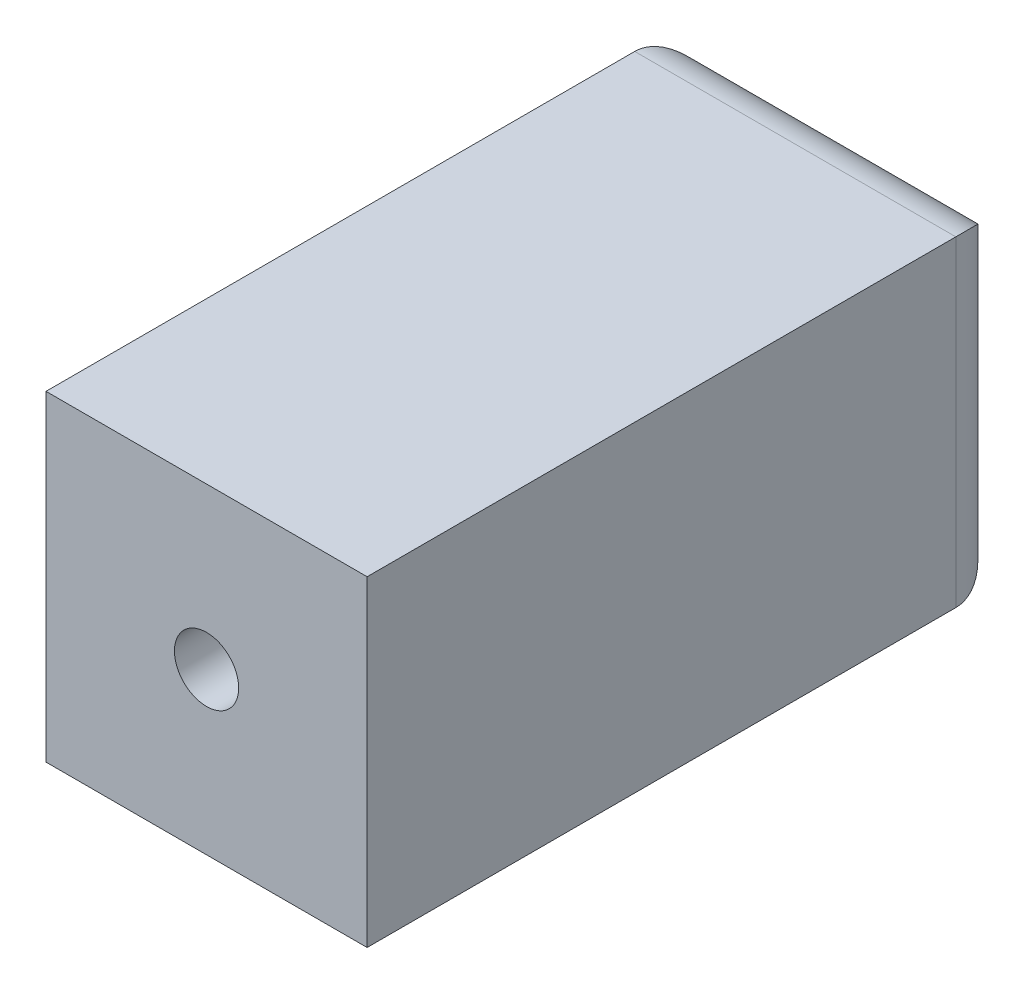
SolidWorks part; units mm, degrees
ref_plane "Front Plane" through (0, 0, 0) normal (0, 0, 1) x (1, 0, 0)
ref_plane "Top Plane" through (0, 0, 0) normal (0, 1, 0) x (1, 0, 0)
ref_plane "Right Plane" through (0, 0, 0) normal (1, 0, 0) x (0, 0, -1)
sketch "Sketch1" plane through (0, 0, 0) normal (0, 0, 1) x (1, 0, 0)
  line L1 (0, 0) -> (15, 0)
  line L2 (0, 0) -> (0, 15)
  line L3 (0, 15) -> (15, 15)
  line L4 (15, 0) -> (15, 15)
  dimension "D1" = 15
  dimension "D2" = 15
extrude "Boss-Extrude1" add sketch "Sketch1" along normal blind 30
fillet "Fillet2" radius 2.5 4 edges at (7.5, 0, 0) (15, 7.5, 0) (7.5, 15, 0) (0, 7.5, 0)
hole_wizard "M3x0.5 Tapped Hole1" positions "Sketch3" profile "Sketch4" tap size "M3x0.5" standard "ANSI Metric" end condition through all
sketch "Sketch3" plane through (0, 0, 0) normal (0, 0, -1) x (-1, 0, 0)
  line L0 (-7.5, 2.5) -> (-7.5, 12.5) construction
  line L1 (-12.5, 2.5) -> (-2.5, 2.5) construction
  line L2 (-2.5, 12.5) -> (-12.5, 12.5) construction
  line L5 (-12.5, 7.5) -> (-2.5, 7.5) construction
  line L6 (-12.5, 12.5) -> (-12.5, 2.5) construction
  line L7 (-2.5, 2.5) -> (-2.5, 12.5) construction
  point P20 (-7.5, 7.5)
sketch "Sketch4" plane through (7.5, 7.5, 0) normal (1, 0, 0) x (0, 1, 0)
  line L0 (0, 0) -> (0, 30)
  line L1 (0, 30) -> (1.5, 30)
  line L2 (1.5, 30) -> (1.5, 0)
  line L5 (1.5, 0) -> (0, 0)
  line L11 (0, -6.35) -> (0, 107.95) construction
  dimension "Thread Major Dia." = 3
  dimension "Thru Tap Drill Depth" = 30
sketch "Sketch5" plane through (0, 0, 0) normal (0, 0, -1) x (-1, 0, 0)
  line L0 (-12.5, 7.5) -> (-2.5, 7.5) construction
  line L1 (-12.5, 12.5) -> (-12.5, 2.5) construction
  line L2 (-2.5, 2.5) -> (-2.5, 12.5) construction
  line L3 (-7.5, 2.5) -> (-7.5, 12.5) construction
  line L4 (-12.5, 2.5) -> (-2.5, 2.5) construction
  line L5 (-2.5, 12.5) -> (-12.5, 12.5) construction
  circle A0 centre (-7.5, 7.5) radius 3
  dimension "D1" = 6
extrude "Cut-Extrude1" cut sketch "Sketch5" against normal blind 27
